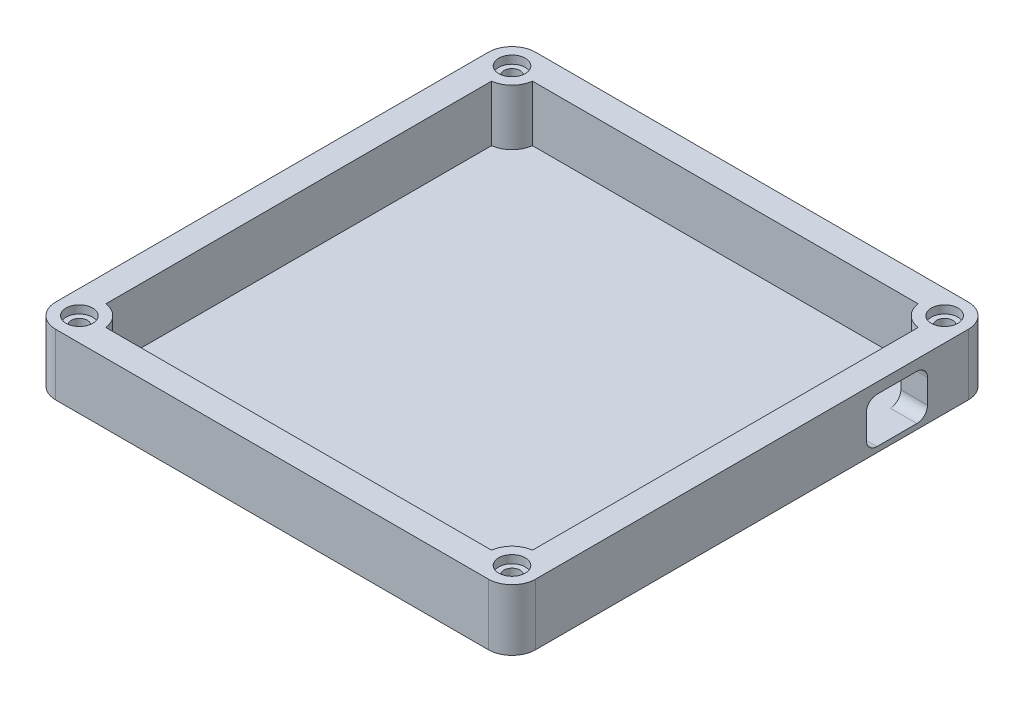
SolidWorks part; units mm, degrees
ref_plane "Front Plane" through (0, 0, 0) normal (0, 0, 1) x (1, 0, 0)
ref_plane "Top Plane" through (0, 0, 0) normal (0, 1, 0) x (1, 0, 0)
ref_plane "Right Plane" through (0, 0, 0) normal (1, 0, 0) x (0, 0, -1)
sketch "Sketch1" plane through (0, 0, 0) normal (0, 1, 0) x (1, 0, 0)
  line L0 (0, 0) -> (0, 40.64)
  line L1 (0, 40.64) -> (40.64, 40.64)
  line L2 (40.64, 40.64) -> (40.64, -40.64)
  line L3 (40.64, -40.64) -> (-40.64, -40.64)
  line L4 (-40.64, -40.64) -> (-40.64, 40.64)
  line L5 (-40.64, 40.64) -> (0, 40.64)
  line L6 (-40.64, -45.0809) -> (40.64, -45.0809)
  line L7 (-45.0809, -40.64) -> (-45.0809, 40.64)
  line L8 (-40.64, 45.0809) -> (40.64, 45.0809)
  line L9 (45.0809, 40.64) -> (45.0809, -40.64)
  line L10 (-45.0809, 18.4234) -> (-40.0809, 18.4234)
  line L11 (-7.938, 45.0809) -> (-7.938, 40.0809)
  line L12 (45.0809, 28.2685) -> (40.0809, 28.2685)
  line L13 (27.0858, -45.0809) -> (27.0858, -40.0809)
  line L14 (27.0858, -40.0809) -> (36.2345, -40.0809)
  line L15 (36.2345, -40.0809) -> (-36.2345, -40.0809)
  line L16 (-40.0809, 18.4234) -> (-40.0809, 36.2345)
  line L17 (-40.0809, 36.2345) -> (-40.0809, -36.2345)
  line L18 (-7.938, 40.0809) -> (-36.2345, 40.0809)
  line L19 (-36.2345, 40.0809) -> (36.2345, 40.0809)
  line L20 (40.0809, 28.2685) -> (40.0809, 36.2345)
  line L21 (40.0809, 36.2345) -> (40.0809, -36.2345)
  arc A0 (40.64, 45.0809) -> (45.0809, 40.64) centre (40.64, 40.64) cw
  arc A1 (-40.64, 45.0809) -> (-45.0809, 40.64) centre (-40.64, 40.64) ccw
  arc A2 (-45.0809, -40.64) -> (-40.64, -45.0809) centre (-40.64, -40.64) ccw
  arc A3 (45.0809, -40.64) -> (40.64, -45.0809) centre (40.64, -40.64) cw
  circle A4 centre (40.64, 40.64) radius 4.4409
  circle A5 centre (-40.64, 40.64) radius 4.4409
  circle A6 centre (-40.64, -40.64) radius 4.4409
  circle A7 centre (40.64, -40.64) radius 4.4409
extrude "Boss-Extrude1" add sketch "Sketch1" along normal blind 11.5 contours A6 L17 L10 L4 | A5 L4 L10 L16 | A5 L18 L11 L5 | A4 L1 L0 L19 | L11 L19 L0 L5 | A4 L20 L12 L2 | A7 L2 L12 L21 | L2 A7 L3 | A7 L14 L13 L3 | A6 L3 L13 L15 | A2 A6 L3 L4 | L3 A6 L4 | A6 L6 L13 L3 | A6 L4 L10 L7 | A3 A7 L2 L3 | A7 L3 L13 L6 | A7 L9 L12 L2 | A4 L2 L12 L9 | L2 A4 A0 L1 | L1 A4 L2 | A4 L8 L11 L5 L1 | A5 L5 L11 L8 | L5 A5 A1 L4 | L4 A5 L5 | A5 L7 L10 L4
sketch "Sketch2" plane through (0, 11.5, 0) normal (0, 1, 0) x (1, 0, 0)
  circle A0 centre (-40.64, 40.64) radius 1.5
  circle A1 centre (40.64, 40.64) radius 1.5
  circle A3 centre (40.64, -40.64) radius 1.5
  circle A4 centre (-40.64, -40.64) radius 1.5
extrude "Cut-Extrude1" cut sketch "Sketch2" against normal blind 8
sketch "Sketch3" plane through (45.0809, 0, 0) normal (1, 0, 0) x (0, 0, -1)
  line L0 (40.64, 11.5) -> (40.64, 0) construction
  line L1 (40.64, 11.5) -> (40.64, 0)
  line L2 (40.64, 11.5) -> (27.229, 11.5)
  line L3 (40.64, 11.5) -> (-40.64, 11.5) construction
  line L4 (27.229, 11.5) -> (27.229, 9.5)
  line L5 (28.6092, 11.5) -> (28.6092, 1)
  line L6 (27.229, 9.5) -> (32.979, 9.5)
  line L7 (32.979, 9.5) -> (32.979, 1)
  line L8 (32.979, 1) -> (27.229, 1)
  line L9 (27.229, 1) -> (21.479, 1)
  line L10 (21.479, 1) -> (21.479, 9.5)
  line L11 (21.479, 9.5) -> (27.229, 9.5)
  line L12 (32.979, 9.5) -> (32.979, 7.5)
  line L13 (32.979, 7.5) -> (30.979, 7.5)
  line L14 (32.979, 1) -> (32.979, 3)
  line L15 (32.979, 3) -> (30.979, 3)
  line L16 (21.479, 1) -> (23.479, 1)
  line L17 (23.479, 1) -> (23.479, 3)
  line L18 (21.479, 9.5) -> (23.479, 9.5)
  line L19 (23.479, 9.5) -> (23.479, 7.5)
  arc A0 (32.979, 7.5) -> (30.979, 9.5) centre (30.979, 7.5) ccw
  arc A1 (32.979, 3) -> (30.979, 1) centre (30.979, 3) cw
  arc A2 (23.479, 1) -> (21.479, 3) centre (23.479, 3) cw
  arc A3 (23.479, 9.5) -> (21.479, 7.5) centre (23.479, 7.5) ccw
extrude "Cut-Extrude2" cut sketch "Sketch3" against normal blind 8
sketch "Sketch4" plane through (0, 11.5, 0) normal (0, 1, 0) x (1, 0, 0)
  circle A0 centre (-40.64, 40.64) radius 2.5
  circle A1 centre (40.64, 40.64) radius 2.5
  circle A2 centre (40.64, -40.64) radius 2.5
  circle A3 centre (-40.64, -40.64) radius 2.5
extrude "Cut-Extrude3" cut sketch "Sketch4" against normal blind 1.5
sketch "Sketch5" plane through (0, 0, 0) normal (0, -1, 0) x (1, 0, 0)
  line L0 (36.2345, -40.0809) -> (-36.2345, -40.0809) construction
  line L1 (40.0809, 36.2345) -> (40.0809, -36.2345) construction
  line L2 (36.2345, 40.0809) -> (-36.2345, 40.0809) construction
  line L3 (-40.0809, 36.2345) -> (-40.0809, -36.2345) construction
  line L4 (40.64, 45.0809) -> (-40.64, 45.0809)
  line L5 (-45.0809, 40.64) -> (-45.0809, -40.64)
  line L6 (-40.64, -45.0809) -> (40.64, -45.0809)
  line L7 (45.0809, -40.64) -> (45.0809, 40.64)
  line L8 (40.64, 45.0809) -> (-40.64, 45.0809)
  line L9 (-45.0809, 40.64) -> (-45.0809, -40.64)
  line L10 (-40.64, -45.0809) -> (40.64, -45.0809)
  line L11 (45.0809, -40.64) -> (45.0809, 40.64)
  line L12 (36.2345, -40.0809) -> (-36.2345, -40.0809)
  line L13 (40.0809, 36.2345) -> (40.0809, -36.2345)
  line L14 (36.2345, 40.0809) -> (-36.2345, 40.0809)
  line L15 (-40.0809, 36.2345) -> (-40.0809, -36.2345)
  arc A0 (40.0809, -36.2345) -> (36.2345, -40.0809) centre (40.64, -40.64) ccw construction
  arc A1 (36.2345, 40.0809) -> (40.0809, 36.2345) centre (40.64, 40.64) ccw construction
  arc A2 (-40.0809, 36.2345) -> (-36.2345, 40.0809) centre (-40.64, 40.64) ccw construction
  arc A3 (40.0809, -36.2345) -> (36.2345, -40.0809) centre (40.64, -40.64) ccw
  arc A4 (-40.64, 45.0809) -> (-45.0809, 40.64) centre (-40.64, 40.64) ccw
  arc A5 (-45.0809, -40.64) -> (-40.64, -45.0809) centre (-40.64, -40.64) ccw
  arc A6 (40.64, -45.0809) -> (45.0809, -40.64) centre (40.64, -40.64) ccw
  arc A7 (45.0809, 40.64) -> (40.64, 45.0809) centre (40.64, 40.64) ccw
  arc A8 (-40.64, 45.0809) -> (-45.0809, 40.64) centre (-40.64, 40.64) ccw
  arc A9 (-45.0809, -40.64) -> (-40.64, -45.0809) centre (-40.64, -40.64) ccw
  arc A10 (40.64, -45.0809) -> (45.0809, -40.64) centre (40.64, -40.64) ccw
  arc A11 (45.0809, 40.64) -> (40.64, 45.0809) centre (40.64, 40.64) ccw
  arc A12 (36.2345, 40.0809) -> (40.0809, 36.2345) centre (40.64, 40.64) ccw
  arc A13 (-40.0809, 36.2345) -> (-36.2345, 40.0809) centre (-40.64, 40.64) ccw
  arc M9 (36.2345, 40.0809) -> (40.0809, 36.2345) centre (40.64, 40.64) ccw
  line M10 (40.0809, 36.2345) -> (40.0809, -36.2345)
  arc M11 (40.0809, -36.2345) -> (36.2345, -40.0809) centre (40.64, -40.64) ccw
  line M12 (36.2345, -40.0809) -> (-36.2345, -40.0809)
  arc M13 (-36.2345, -40.0809) -> (-40.0809, -36.2345) centre (-40.64, -40.64) ccw
  line M14 (-40.0809, -36.2345) -> (-40.0809, 36.2345)
  arc M15 (-40.0809, 36.2345) -> (-36.2345, 40.0809) centre (-40.64, 40.64) ccw
  line M16 (-36.2345, 40.0809) -> (36.2345, 40.0809)
  dimension "D1" = 0
extrude "Boss-Extrude2" add sketch "Sketch5" against normal up to surface (1 mm away) contours M9 M16 M15 M14 M13 M12 M11 M10 up to face at (42.5809, 1, -27.229)
